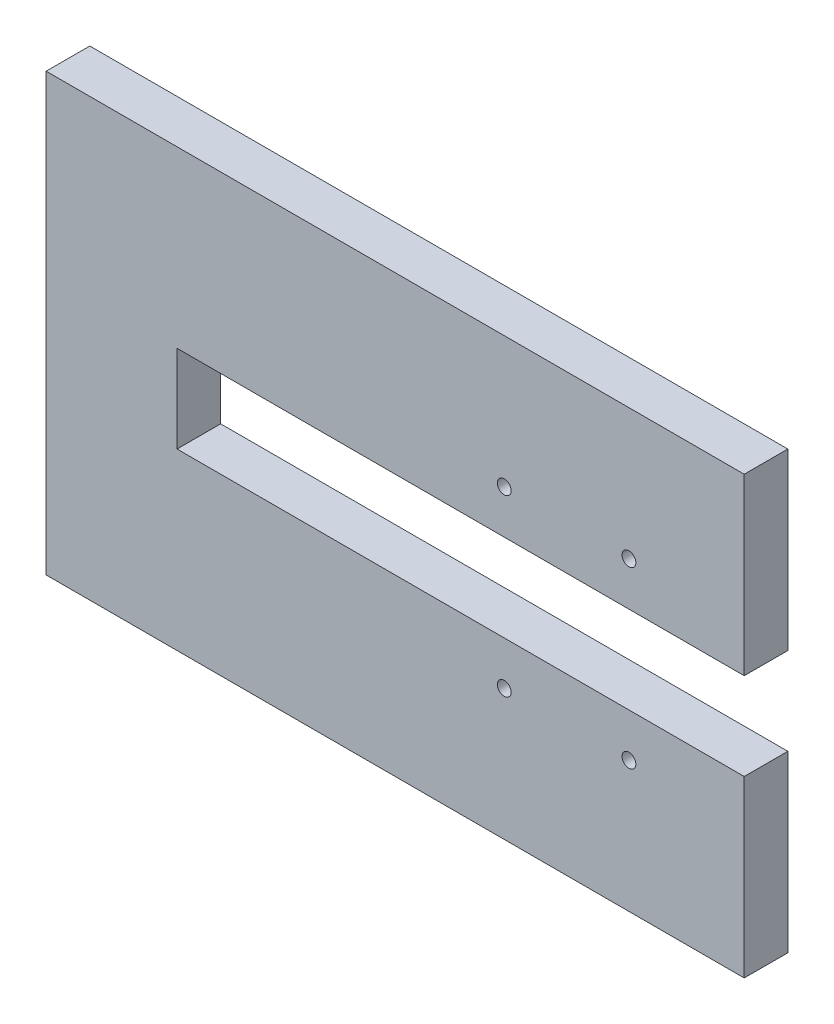
SolidWorks part; units mm, degrees
ref_plane "Front Plane" through (0, 0, 0) normal (0, 0, 1) x (1, 0, 0)
ref_plane "Top Plane" through (0, 0, 0) normal (0, 1, 0) x (1, 0, 0)
ref_plane "Right Plane" through (0, 0, 0) normal (1, 0, 0) x (0, 0, -1)
sketch "Sketch1" plane through (0, 0, 0) normal (0, 0, 1) x (1, 0, 0)
  line L0 (-53.5376, 64.885) -> (106.4624, 64.885)
  line L1 (-53.5376, -35.115) -> (106.4624, -35.115)
  line L2 (-53.5376, 64.885) -> (-53.5376, -35.115)
  line L3 (106.4624, 64.885) -> (106.4624, 24.885)
  line L4 (106.4624, -35.115) -> (106.4624, 4.885)
  line L5 (106.4624, 4.885) -> (-23.5376, 4.885)
  line L6 (106.4624, 24.885) -> (-23.5376, 24.885)
  line L7 (-23.5376, 24.885) -> (-23.5376, 4.885)
  circle A0 centre (51.4624, 34.885) radius 1.5875
  circle A1 centre (80.0374, 34.885) radius 1.5875
  circle A2 centre (51.4624, -5.115) radius 1.5875
  circle A3 centre (80.0374, -5.115) radius 1.5875
  dimension "D3" = 55
  dimension "D4" = 3.175
  dimension "D7" = 10
  dimension "D1" = 100
  dimension "D2" = 160
  dimension "D5" = 28.575
  dimension "D6" = 10
  dimension "D8" = 40
  dimension "D9" = 130
extrude "Boss-Extrude1" add sketch "Sketch1" along normal blind 10
